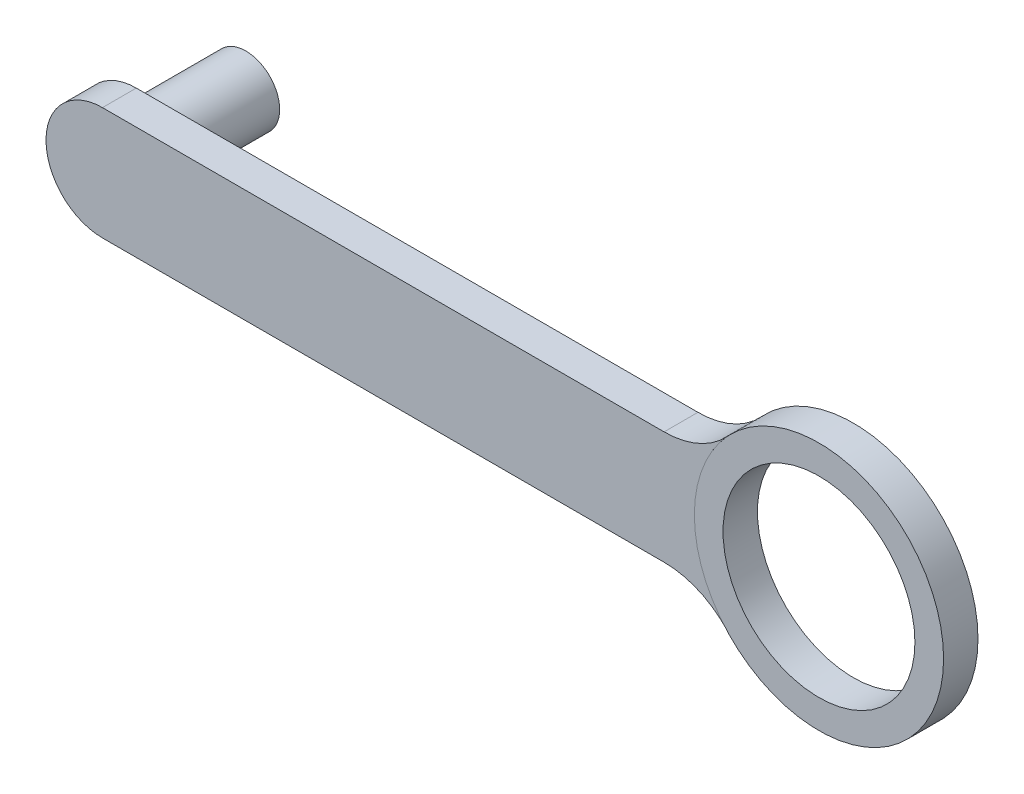
SolidWorks part; units mm, degrees
ref_plane "Front Plane" through (0, 0, 0) normal (0, 0, 1) x (1, 0, 0)
ref_plane "Top Plane" through (0, 0, 0) normal (0, 1, 0) x (1, 0, 0)
ref_plane "Right Plane" through (0, 0, 0) normal (1, 0, 0) x (0, 0, -1)
sketch "Sketch1" plane through (0, 0, 0) normal (0, 0, 1) x (1, 0, 0)
  line L0 (-31.75, 0) -> (31.75, 0) construction
  line L1 (-31.75, 5) -> (31.75, 5)
  line L2 (-31.75, -5) -> (31.75, -5)
  arc A0 (-31.75, 5) -> (-31.75, -5) centre (-31.75, 0) ccw
  arc A1 (31.75, -5) -> (31.75, 5) centre (31.75, 0) ccw
  circle A2 centre (-31.75, 0) radius 3
  circle A3 centre (31.75, 0) radius 3
  point P2 (0, 0)
  dimension "D1" = 63.5
  dimension "D2" = 5
  dimension "D3" = 6
extrude "Boss-Extrude1" add sketch "Sketch1" along normal mid plane 3
sketch "Sketch2" plane through (0, 0, 1.5) normal (0, 0, 1) x (1, 0, 0)
  circle A0 centre (-31.75, 0) radius 3 construction
  circle A1 centre (-31.75, 0) radius 3
extrude "Boss-Extrude2" add sketch "Sketch2" against normal blind 12.7
sketch "Sketch3" plane through (0, 0, 0) normal (0, 0, 1) x (1, 0, 0)
  circle A0 centre (31.75, 0) radius 8.5 construction
  circle A1 centre (31.75, 0) radius 11.04
  dimension "D1" = 17
  dimension "D2" = 2.54
extrude "Boss-Extrude3" add sketch "Sketch3" against normal mid plane 3.048
fillet "Fillet1" radius 7.62 2 edges at (21.9072, -5, 0) (21.9072, 5, 0)
sketch "Sketch4" plane through (0, 0, 1.524) normal (0, 0, 1) x (1, 0, 0)
  circle A0 centre (31.75, 0) radius 8.5
  dimension "D1" = 17
extrude "Cut-Extrude1" cut sketch "Sketch4" against normal through all
